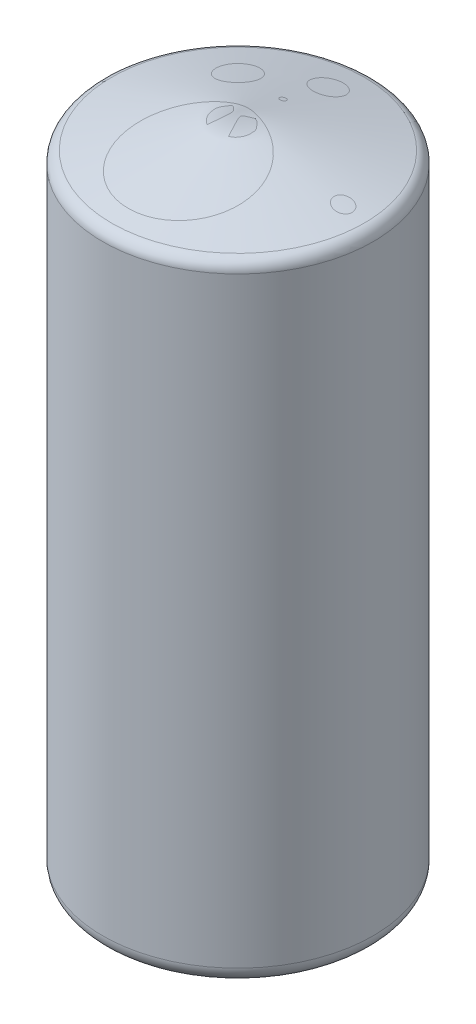
SolidWorks part; units mm, degrees
material "1.4301 V2A"
ref_plane "Ebene vorne" through (0, 0, 0) normal (0, 0, 1) x (1, 0, 0)
ref_plane "Ebene oben" through (0, 0, 0) normal (0, 1, 0) x (1, 0, 0)
ref_plane "Ebene rechts" through (0, 0, 0) normal (1, 0, 0) x (0, 0, -1)
sketch "Skizze1" plane through (0, 0, 0) normal (0, 0, 1) x (1, 0, 0)
  line L0 (0, 0) -> (0, 2500) construction
  line L1 (-75, 27.2978) -> (-413.8111, 150.6149)
  line L2 (-450, 202.298) -> (-450, 2202.298)
  line L3 (-420.3528, 2240.9351) -> (0, 2353.5682)
  line L5 (-75, 29.9582) -> (-412.9561, 152.9642)
  line L8 (-447.5, 202.298) -> (-447.5, 2202.298)
  line L9 (-419.7057, 2238.5202) -> (0, 2350.98)
  line L10 (-75, 27.2978) -> (-75, 29.9582)
  line L11 (0, 2353.5682) -> (0, 2350.98)
  line L12 (-74.1449, 29.647) -> (-412.9561, 152.9642) construction
  line L14 (-419.7057, 2238.5202) -> (0.647, 2351.1534) construction
  line L15 (-450, 202.298) -> (-450, 2202.298) construction
  arc A0 (-413.8111, 150.6149) -> (-450, 202.298) centre (-395, 202.298) cw
  arc A1 (-450, 2202.298) -> (-420.3528, 2240.9351) centre (-410, 2202.298) cw
  arc A2 (-412.9561, 152.9642) -> (-447.5, 202.298) centre (-395, 202.298) cw
  arc A3 (-447.5, 2202.298) -> (-419.7057, 2238.5202) centre (-410, 2202.298) cw
  dimension "D6" = 55
  dimension "D7" = 40
  dimension "D1" = 150
  dimension "D2" = 2500
  dimension "D3" = 105
  dimension "D4" = 2000
  dimension "D8" = 2.5
revolve "Rotation4" add sketch "Skizze1" angle 360 about L0
ref_plane "Ebene1" through (0, 2353.5682, 0) normal (0, 1, 0) x (1, 0, 0)
sketch "Skizze3" plane through (0, 2353.5682, 0) normal (0, 1, 0) x (1, 0, 0)
  line L0 (0, 550.0873) -> (0, -541.5964) construction
  line L1 (0, 0) -> (-462.7542, 462.7542) construction
  line L2 (630.1441, 0) -> (-662.8946, 0) construction
  circle A0 centre (0, -165) radius 200
  circle A1 centre (350, 0) radius 30
  circle A2 centre (-176.7767, 176.7767) radius 62.5
  circle A3 centre (0, 300) radius 50
  circle A4 centre (0, 0) radius 300 construction
  circle A5 centre (0, 150) radius 10
  circle A6 centre (0, 0) radius 250 construction
  dimension "D3" = 350
  dimension "D4" = 600
  dimension "D5" = 150
  dimension "D2" = 45
split line "Trennlinie2"
sketch3d "3D-Skizze1"
  spline S0 degree 3 number of poles 119 (330.387, 2264.8326, -22.7008) -> (330.387, 2264.8326, -22.7008) construction
  spline S1 degree 3 number of poles 119 (330.387, 2264.8326, -22.7008) -> (330.387, 2264.8326, -22.7008)
  spline S2 degree 3 number of poles 131 (-34.2547, 2262.958, -336.4228) -> (-34.2547, 2262.958, -336.4228) construction
  spline S3 degree 3 number of poles 131 (-34.2547, 2262.958, -336.4228) -> (-34.2547, 2262.958, -336.4228)
  spline S4 degree 3 number of poles 137 (-220.9709, 2269.8341, -220.9709) -> (-220.9709, 2269.8341, -220.9709) construction
  spline S5 degree 3 number of poles 137 (-220.9709, 2269.8341, -220.9709) -> (-220.9709, 2269.8341, -220.9709)
  spline S6 degree 3 number of poles 211 (-167.0043, 2306.4589, 54.9565) -> (-167.0043, 2306.4589, 54.9565) construction
  spline S7 degree 3 number of poles 211 (-167.0043, 2306.4589, 54.9565) -> (-167.0043, 2306.4589, 54.9565)
  spline S8 degree 3 number of poles 93 (-6.7388, 2311.3575, -157.3884) -> (-6.7388, 2311.3575, -157.3884) construction
  spline S9 degree 3 number of poles 93 (-6.7388, 2311.3575, -157.3884) -> (-6.7388, 2311.3575, -157.3884)
